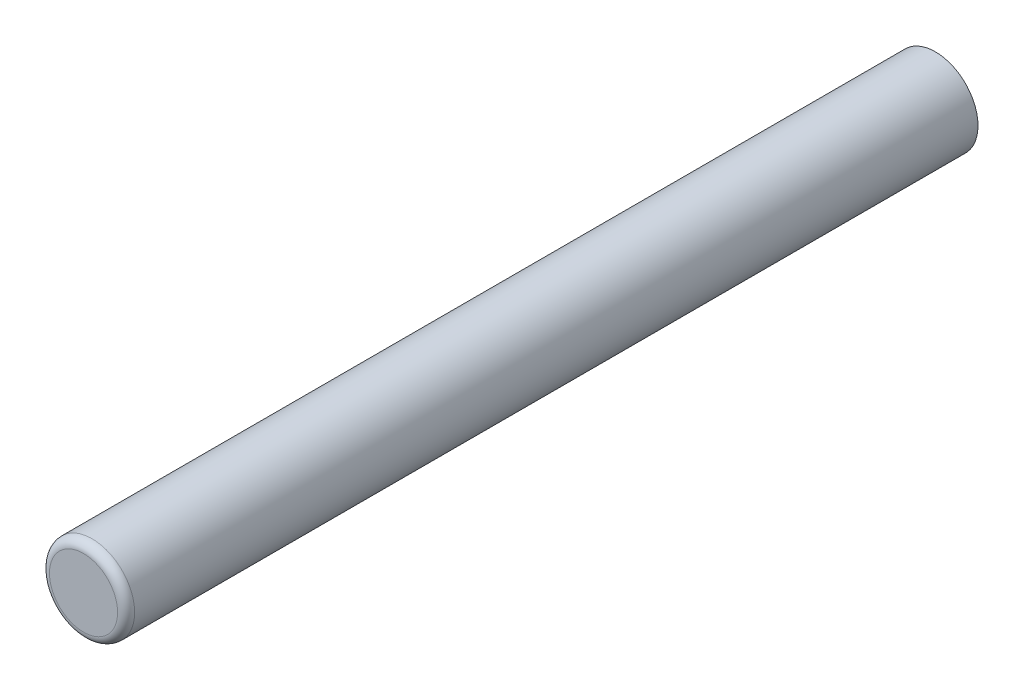
SolidWorks part; units mm, degrees
ref_plane "Front Plane" through (0, 0, 0) normal (0, 0, 1) x (1, 0, 0)
ref_plane "Top Plane" through (0, 0, 0) normal (0, 1, 0) x (1, 0, 0)
ref_plane "Right Plane" through (0, 0, 0) normal (1, 0, 0) x (0, 0, -1)
sketch "Sketch1" plane through (0, 0, 0) normal (0, 0, 1) x (1, 0, 0)
  circle A0 centre (0, 0) radius 3.175
  dimension "D1" = 6.35
extrude "Boss-Extrude1" add sketch "Sketch1" along normal blind 63.5
fillet "Fillet1" radius 0.635 1 edges at (3.175, 0, 63.5)
